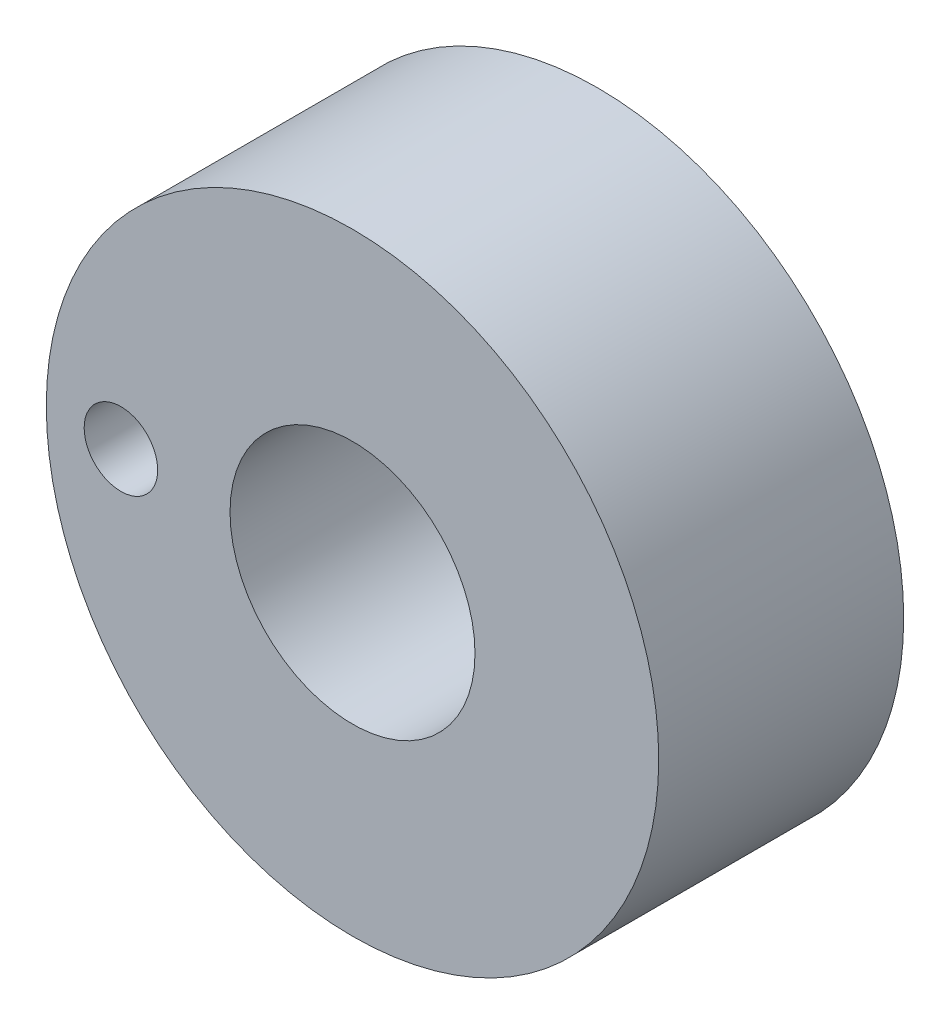
SolidWorks part; units mm, degrees
ref_plane "Front Plane" through (0, 0, 0) normal (0, 0, 1) x (1, 0, 0)
ref_plane "Top Plane" through (0, 0, 0) normal (0, 1, 0) x (1, 0, 0)
ref_plane "Right Plane" through (0, 0, 0) normal (1, 0, 0) x (0, 0, -1)
sketch "Sketch1" plane through (0, 0, 0) normal (0, 0, 1) x (1, 0, 0)
  circle A0 centre (0, 0) radius 25
  dimension "D1" = 50
extrude "Boss-Extrude1" add sketch "Sketch1" along normal blind 20 contours A0
sketch "Sketch3" plane through (0, 0, 0) normal (0, 0, -1) x (-1, 0, 0)
  circle A0 centre (0, 0) radius 10
  circle A1 centre (18.9082, 0) radius 3
extrude "Cut-Extrude2" cut sketch "Sketch3" against normal through all
